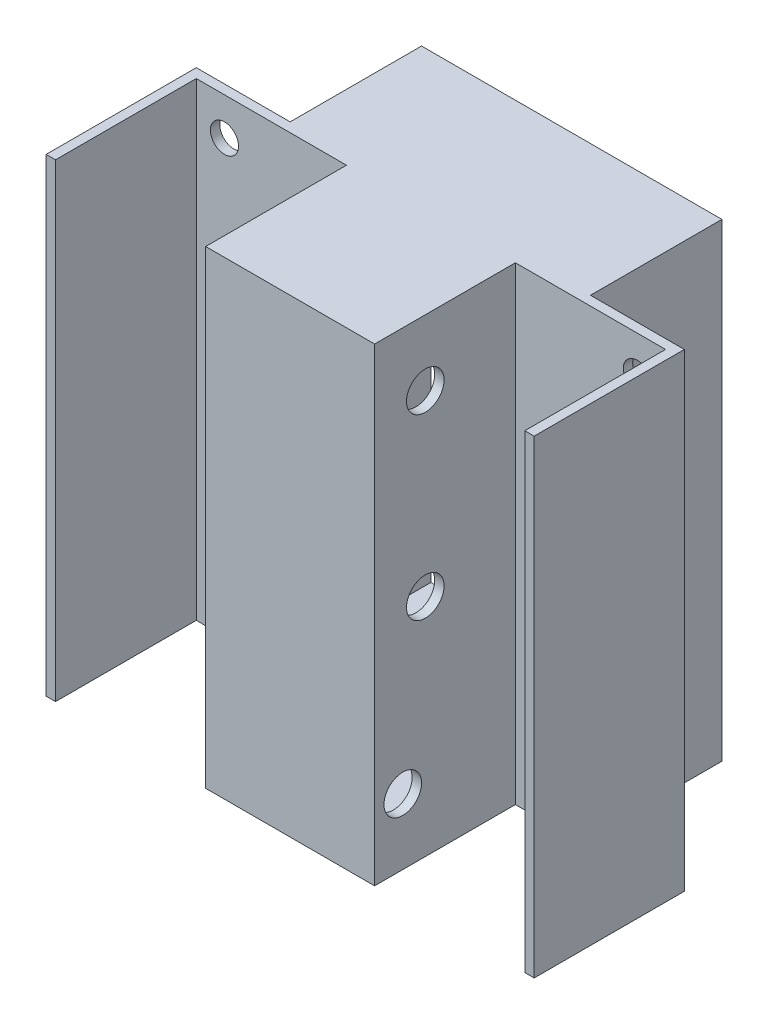
SolidWorks part; units mm, degrees
ref_plane "Plan de face" through (0, 0, 0) normal (0, 0, 1) x (1, 0, 0)
ref_plane "Plan de dessus" through (0, 0, 0) normal (0, 1, 0) x (1, 0, 0)
ref_plane "Plan de droite" through (0, 0, 0) normal (1, 0, 0) x (0, 0, -1)
sketch "Esquisse1" plane through (0, 0, 0) normal (0, 0, 1) x (1, 0, 0)
  line L1 (0, 0) -> (-90, 0)
  line L2 (0, 0) -> (0, 250)
  line L3 (0, 250) -> (-90, 250)
  line L4 (-90, 0) -> (-90, 250)
  dimension "D1" = 250
  dimension "D2" = 90
extrude "Boss.-Extru.1" add sketch "Esquisse1" along normal blind 5
sketch "Esquisse2" plane through (0, 0, 0) normal (0, 0, -1) x (-1, 0, 0)
  line L0 (5, 245) -> (5, 5)
  line L1 (0, 250) -> (90, 250)
  line L2 (0, 250) -> (0, 0)
  line L3 (0, 0) -> (90, 0)
  line L4 (90, 250) -> (90, 0)
  line L5 (5, 5) -> (85, 5)
  line L6 (85, 245) -> (85, 5)
  line L7 (5, 245) -> (85, 245)
  dimension "D1" = 5
extrude "Boss.-Extru.2" add sketch "Esquisse2" along normal blind 70
sketch "Esquisse3" plane through (0, 0, -70) normal (0, 0, -1) x (-1, 0, 0)
  line L0 (90, 250) -> (0, 250) construction
  line L1 (6.0255, 250) -> (-80, 250)
  line L2 (5, 245) -> (5, 5)
  line L3 (-15, 0) -> (-80, 0)
  line L4 (-80, 250) -> (-80, 0)
  line L5 (85, 245) -> (5, 245) construction
  line L6 (45, 245) -> (5, 245)
  line L7 (45, 245) -> (45, 250)
  line L8 (45, 250) -> (6.0255, 250)
  line L9 (5, 245) -> (5, 5) construction
  line L10 (5, 5) -> (85, 5) construction
  line L11 (45, 5) -> (5, 5)
  line L12 (45, 5) -> (45, 0)
  line L13 (45, 0) -> (-15, 0)
  line L14 (0, 250) -> (0, 0) construction
  dimension "D1" = 80
extrude "Boss.-Extru.3" add sketch "Esquisse3" along normal blind 5
mirror "Symétrie1" about plane through (-45, 245, -75) normal (1, 0, 0) of "Boss.-Extru.3"
sketch "Esquisse4" plane through (-90, 0, 0) normal (-1, 0, 0) x (0, 0, 1)
  line L0 (5, 250) -> (5, 0) construction
  line L1 (5, 250) -> (-70, 250) construction
  line L2 (5, 0) -> (-70, 0) construction
  circle A0 centre (-22, 215) radius 30
  circle A1 centre (-22, 215) radius 10
  circle A2 centre (-22, 120) radius 10
  circle A3 centre (-10, 35) radius 10
  circle A4 centre (-22, 25) radius 10 [skipped]
  dimension "D1" = 27
  dimension "D3" = 60
  dimension "D4" = 20
  dimension "D6" = 20
  dimension "D2" = 35
  dimension "D7" = 15
  dimension "D8" = 35
  dimension "D5" = 3
extrude "Enlèv. mat.-Extru.2" cut sketch "Esquisse4" against normal through all contours A1 | A2 | A3
sketch "Esquisse5" plane through (80, 0, 0) normal (1, 0, 0) x (0, 0, -1)
  line L1 (75, 250) -> (-5, 250)
  line L2 (75, 250) -> (75, 0)
  line L3 (75, 0) -> (-5, 0)
  line L4 (-5, 250) -> (-5, 0)
extrude "Boss.-Extru.4" add sketch "Esquisse5" along normal blind 5
sketch "Esquisse6" plane through (-170, 0, 0) normal (-1, 0, 0) x (0, 0, 1)
  line L1 (-75, 250) -> (5, 250)
  line L2 (-75, 250) -> (-75, 0)
  line L3 (-75, 0) -> (5, 0)
  line L4 (5, 250) -> (5, 0)
extrude "Boss.-Extru.5" add sketch "Esquisse6" along normal blind 5
sketch "Esquisse7" plane through (0, 0, -75) normal (0, 0, -1) x (-1, 0, 0)
  line L0 (175, 250) -> (-85, 250) construction
  line L1 (-35, 250) -> (125, 250)
  line L2 (-35, 250) -> (-35, 0)
  line L3 (-35, 0) -> (125, 0)
  line L4 (125, 250) -> (125, 0)
  line L5 (-85, 0) -> (175, 0) construction
  line L6 (-85, 0) -> (-85, 250) construction
  line L7 (175, 250) -> (175, 0) construction
  line L8 (-30, 245) -> (120, 245)
  line L9 (120, 245) -> (120, 5)
  line L10 (-30, 5) -> (120, 5)
  line L11 (-30, 245) -> (-30, 5)
  dimension "D1" = 50
  dimension "D2" = 50
  dimension "D3" = 5
extrude "Boss.-Extru.6" add sketch "Esquisse7" along normal blind 70
sketch "Esquisse10" plane through (0, 0, -75) normal (0, 0, -1) x (-1, 0, 0)
  line L0 (-35, 250) -> (-85, 250) construction
  line L1 (175, 250) -> (125, 250) construction
  line L2 (175, 250) -> (175, 0) construction
  line L3 (-85, 0) -> (-85, 250) construction
  circle A0 centre (155, 230) radius 7.5
  circle A1 centre (-65, 230) radius 7.5
  circle A2 centre (-65, 160) radius 7.5
  circle A3 centre (155, 160) radius 7.5
  circle A4 centre (-65, 90) radius 7.5
  circle A5 centre (155, 90) radius 7.5
  circle A6 centre (-65, 20) radius 7.5
  circle A7 centre (155, 20) radius 7.5
  point P4 (-60, 250)
  dimension "D1" = 15
  dimension "D2" = 15
  dimension "D5" = 20
  dimension "D3" = 20
  dimension "D4" = 20
  dimension "D6" = 20
  dimension "D7" = 4
extrude "Enlèv. mat.-Extru.3" cut sketch "Esquisse10" against normal blind 50
